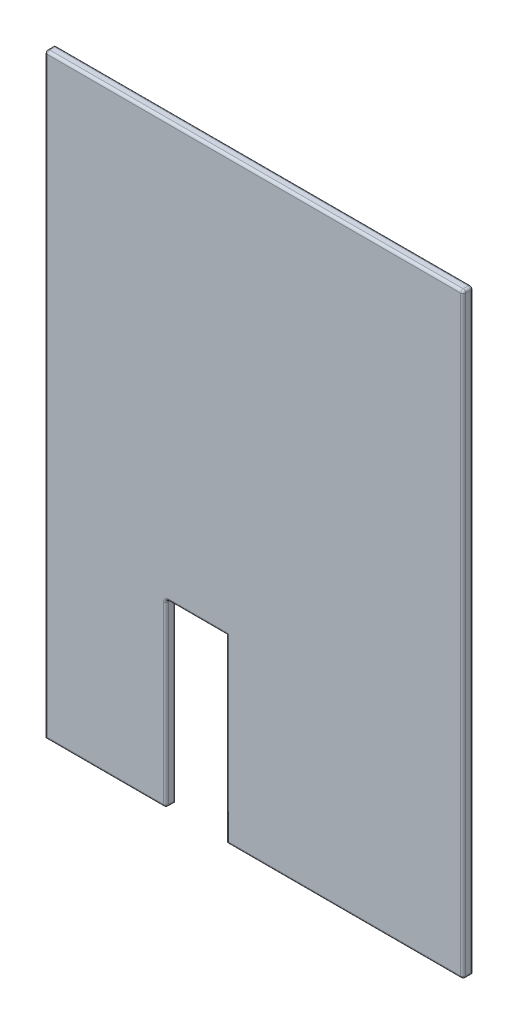
SolidWorks part; units mm, degrees
material "1060 Alloy"
ref_plane "Front Plane" through (0, 0, 0) normal (0, 0, 1) x (1, 0, 0)
ref_plane "Top Plane" through (0, 0, 0) normal (0, 1, 0) x (1, 0, 0)
ref_plane "Right Plane" through (0, 0, 0) normal (1, 0, 0) x (0, 0, -1)
sketch "Sketch1" plane through (0, 0, 0) normal (0, 0, 1) x (1, 0, 0)
  line L0 (-175.5, -595) -> (-175.5, -235)
  line L1 (-417.5, 595) -> (417.5, 595)
  line L2 (-417.5, 595) -> (-417.5, -595)
  line L3 (-417.5, -595) -> (-175.5, -595)
  line L4 (417.5, 595) -> (417.5, -595)
  line L5 (-417.5, 595) -> (417.5, -595) construction
  line L6 (-417.5, -595) -> (417.5, 595) construction
  line L7 (-175.5, -235) -> (-55.5, -235)
  line L8 (-55.5, -235) -> (-55.5, -595)
  line L9 (-115.5, -235) -> (-115.5, -284.6033) construction
  line L10 (-55.5, -595) -> (417.5, -595)
  point P0 (0, 0)
  dimension "D1" = 120
  dimension "D2" = 302
  dimension "D3" = 1190
  dimension "D4" = 835
  dimension "D5" = 360
extrude "Boss-Extrude1" add sketch "Sketch1" along normal blind 20
fillet "Fillet1" radius 5 17 edges at (-115.5, -235, 0) (417.5, 0, 0) (0, 595, 0) (-175.5, -415, 0) (181, -595, 20) (417.5, 0, 20) (0, 595, 20) (-417.5, 0, 20) (-296.5, -595, 20) (-175.5, -415, 20) (-115.5, -235, 20) (-55.5, -415, 20) (-175.5, -235, 10) (-175.5, -595, 10) (-417.5, 595, 10) (417.5, 595, 10) (417.5, -595, 10)
